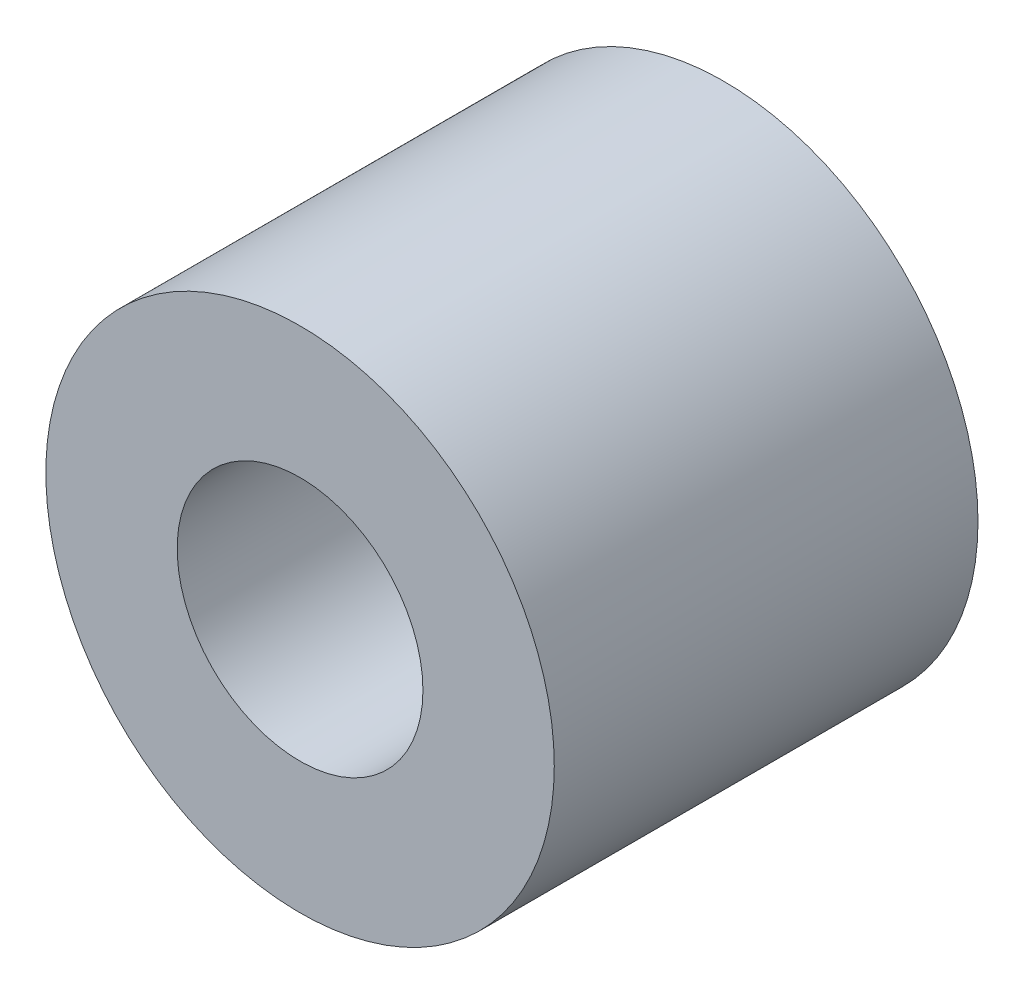
SolidWorks part; units mm, degrees
ref_plane "Front" through (0, 0, 0) normal (0, 0, 1) x (1, 0, 0)
ref_plane "Top" through (0, 0, 0) normal (0, 1, 0) x (1, 0, 0)
ref_plane "Right" through (0, 0, 0) normal (1, 0, 0) x (0, 0, -1)
sketch "Эскиз1" plane through (0, 0, 0) normal (0, 0, 1) x (1, 0, 0)
  circle A0 centre (0, 0) radius 3
  circle A1 centre (0, 0) radius 1.45
  dimension "D1" = 2.9
  dimension "D2" = 6
extrude "Бобышка-Вытянуть1" add sketch "Эскиз1" along normal blind 5
